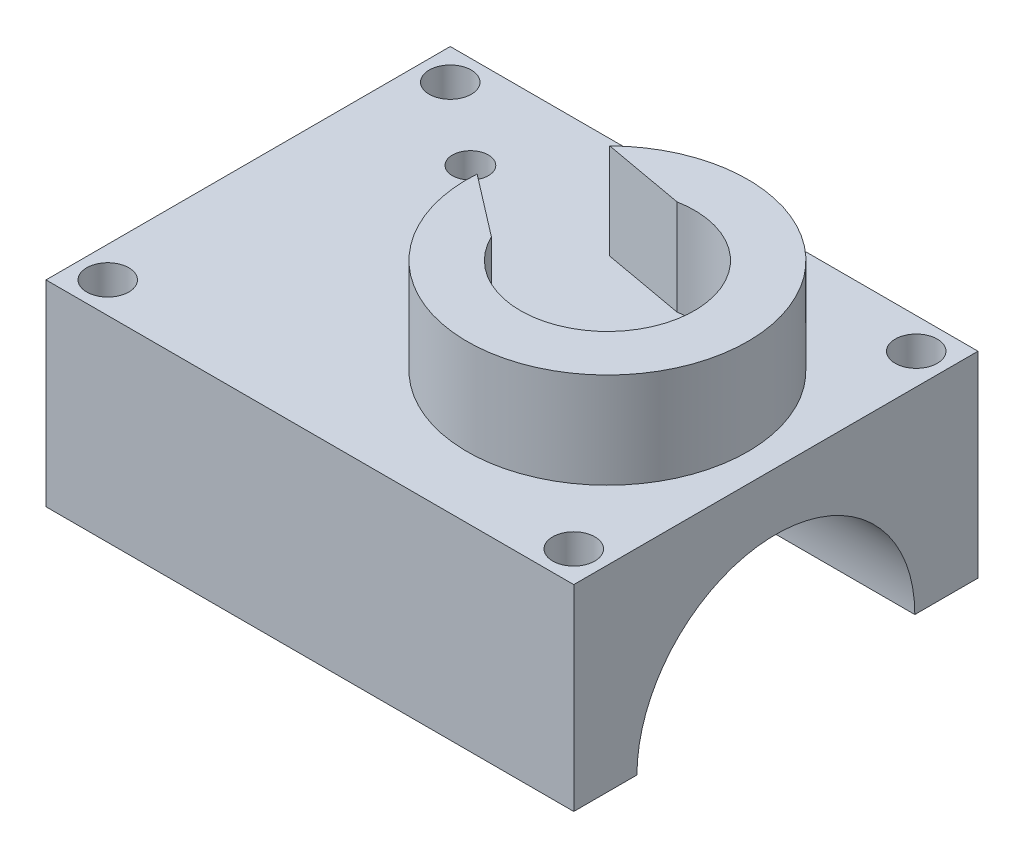
SolidWorks part; units mm, degrees
ref_plane "Front Plane" through (0, 0, 0) normal (0, 0, 1) x (1, 0, 0)
ref_plane "Top Plane" through (0, 0, 0) normal (0, 1, 0) x (1, 0, 0)
ref_plane "Right Plane" through (0, 0, 0) normal (1, 0, 0) x (0, 0, -1)
sketch "Sketch1" plane through (0, 0, 0) normal (0, 1, 0) x (1, 0, 0)
  line L1 (-30, -18) -> (30, -18)
  line L2 (-30, -18) -> (-30, 18)
  line L3 (-30, 18) -> (30, 18)
  line L4 (30, -18) -> (30, 18)
  line L5 (-30, -18) -> (30, 18) construction
  line L6 (-30, 18) -> (30, -18) construction
  point P0 (0, 0)
  dimension "D1" = 60
  dimension "D2" = 36
extrude "Boss-Extrude1" add sketch "Sketch1" along normal blind 35
sketch "Sketch3" plane through (30, 0, 0) normal (1, 0, 0) x (0, 0, -1)
  line L0 (0, 0) -> (0, 35) construction
  line L1 (-18, 0) -> (18, 0) construction
  line L2 (-18, 35) -> (18, 35) construction
  circle A0 centre (0, 17.5) radius 12.375
  dimension "D1" = 24.75
extrude "Cut-Extrude1" cut sketch "Sketch3" against normal through all
sketch "Sketch5" plane through (0, 35, 0) normal (0, 1, 0) x (1, 0, 0)
  line L0 (30, -18) -> (30, 18) construction
  line L5 (-17, 18) -> (-17, -18) construction
  line L6 (30, 18) -> (-30, 18) construction
  line L7 (-30, -18) -> (30, -18) construction
  line L10 (0, 0) -> (0, 2.7791) construction
  line L11 (0, 2.7791) -> (0, 0) construction
  line L12 (0, 0) -> (-2.7536, 0) construction
  circle A3 centre (27.25, -15.25) radius 1.875
  circle A4 centre (27.25, 15.25) radius 1.875
  circle A5 centre (-14.25, -15.25) radius 1.875
  circle A6 centre (-14.25, 15.25) radius 1.875
  point P0 (0, 0)
  dimension "D1" = 2.75
  dimension "D2" = 2.75
  dimension "D3" = 47
  dimension "D4" = 2.75
extrude "Cut-Extrude2" cut sketch "Sketch5" against normal blind 40
sketch "Sketch7" plane through (0, 0, 0) normal (1, 0, 0) x (0, 0, -1)
  line L0 (-18, 35) -> (-18, 0) construction
  line L1 (-18, 17.5) -> (18, 17.5)
  line L2 (-18, 17.5) -> (-18, 0)
  line L3 (-18, 0) -> (18, 0)
  line L4 (18, 17.5) -> (18, 0)
extrude "Cut-Extrude3" cut sketch "Sketch7" against normal through all from surface at 30 starting at face at (30, 17.5, -12.375)
sketch "Sketch19" plane through (0, 17.5, 0) normal (0, -1, 0) x (1, 0, 0)
  line L0 (0, 0) -> (30, 0) construction
  line L1 (30, -12.375) -> (30, 12.375) construction
  circle A0 centre (15, 0) radius 2.885
  dimension "D1" = 5.77
extrude "Cut-Extrude13" cut sketch "Sketch19" against normal blind 14
sketch "Sketch20" plane through (0, 31.5, 0) normal (0, -1, 0) x (1, 0, 0)
  circle A0 centre (15, 0) radius 1.6
  dimension "D1" = 3.2
extrude "Cut-Extrude14" cut sketch "Sketch20" against normal blind 13
sketch "Sketch21" plane through (0, 35, 0) normal (0, 1, 0) x (1, 0, 0)
  line L0 (15, 0) -> (-6.9378, 9.7331) construction
  circle A0 centre (-6.9378, 9.7331) radius 1.6
  dimension "D2" = 3.2
  dimension "D1" = 24
extrude "Cut-Extrude15" cut sketch "Sketch21" against normal through all
sketch "Sketch22" plane through (0, 17.5, 0) normal (0, -1, 0) x (1, 0, 0)
  line L0 (-30, -12.375) -> (30, -12.375) construction
  line L1 (-9.8046, -12.375) -> (-4.1046, -12.375)
  line L2 (-9.8046, -12.375) -> (-9.8046, -5.5699)
  line L3 (-9.8046, -5.5699) -> (-4.1046, -5.5699)
  line L4 (-4.1046, -12.375) -> (-4.1046, -5.5699)
  dimension "D1" = 5.7
extrude "Cut-Extrude16" cut sketch "Sketch22" against normal blind 12
sketch "Sketch23" plane through (0, 35, 0) normal (0, 1, 0) x (1, 0, 0)
  circle A0 centre (15, 0) radius 7.75
  circle A1 centre (15, 0) radius 12.5
  dimension "D1" = 15.5
  dimension "D2" = 25
extrude "Boss-Extrude2" add sketch "Sketch23" along normal blind 8.5
sketch "Sketch24" plane through (0, 43.5, 0) normal (0, 1, 0) x (1, 0, 0)
  line L4 (-6.9378, 8.1331) -> (13.5742, -7.6177)
  line L5 (-6.3175, 11.2079) -> (13.5742, 7.6177)
  line L6 (-6.3175, 11.2079) -> (-6.9378, 8.1331)
  line L7 (13.5742, 7.6177) -> (13.5742, -7.6177)
  circle A2 centre (-6.9378, 9.7331) radius 1.6 construction
  circle A3 centre (15, 0) radius 7.75 construction
  circle A4 centre (15, 0) radius 7.75 construction
extrude "Cut-Extrude17" cut sketch "Sketch24" against normal blind 8.5
sketch "Sketch25" plane through (-30, 0, 0) normal (-1, 0, 0) x (0, 0, 1)
  line L1 (-20.4834, 36.1403) -> (19.9015, 36.1403)
  line L2 (-20.4834, 36.1403) -> (-20.4834, 15.6569)
  line L3 (-20.4834, 15.6569) -> (19.9015, 15.6569)
  line L4 (19.9015, 36.1403) -> (19.9015, 15.6569)
extrude "Cut-Extrude18" cut sketch "Sketch25" against normal blind 13
